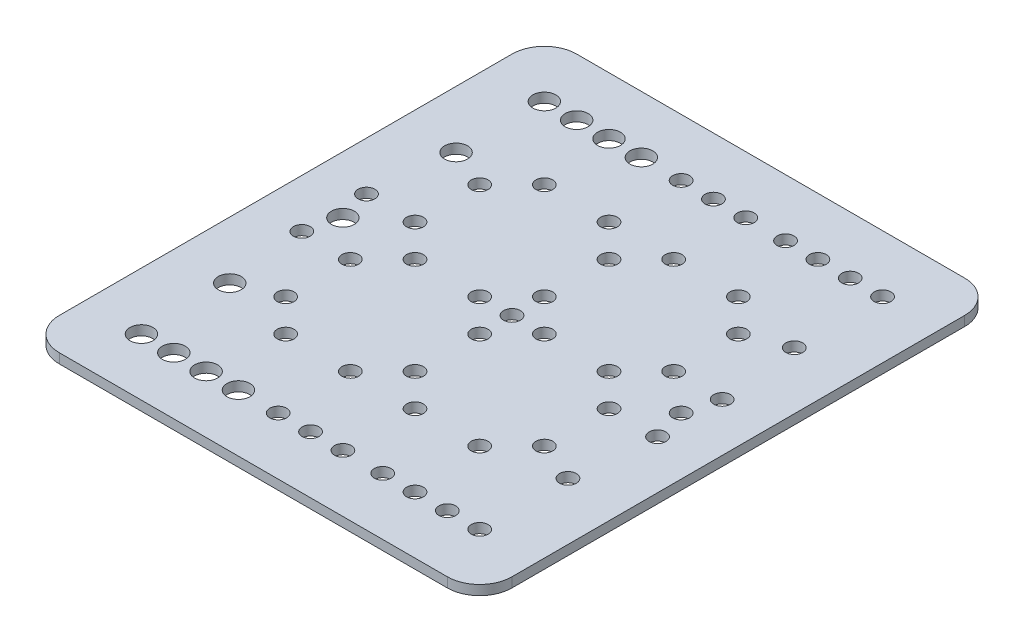
SolidWorks part; units mm, degrees
material "6061-T6 (SS)"
ref_plane "Front Plane" through (0, 0, 0) normal (0, 0, 1) x (1, 0, 0)
ref_plane "Top Plane" through (0, 0, 0) normal (0, 1, 0) x (1, 0, 0)
ref_plane "Right Plane" through (0, 0, 0) normal (1, 0, 0) x (0, 0, -1)
sketch "Sketch1" plane through (0, 0, 0) normal (0, 1, 0) x (1, 0, 0)
  line L0 (0, 0) -> (70, 0) construction
  line L1 (60, -80) -> (-60, -80)
  line L2 (70, -70) -> (70, 70)
  line L3 (60, 80) -> (-60, 80)
  line L4 (-70, -70) -> (-70, 70)
  line L5 (0, 80) -> (0, 0) construction
  arc A0 (-60, -80) -> (-70, -70) centre (-60, -70) cw
  arc A1 (60, -80) -> (70, -70) centre (60, -70) ccw
  arc A2 (70, 70) -> (60, 80) centre (60, 70) ccw
  arc A3 (-60, 80) -> (-70, 70) centre (-60, 70) ccw
  circle A4 centre (-42.3, 62.3) radius 3.55
  circle A5 centre (0, 10) radius 2.6
  circle A6 centre (0, 0) radius 2.6
  circle A7 centre (10, 0) radius 2.6
  circle A8 centre (-10, 0) radius 2.6
  circle A9 centre (-52.3, 62.3) radius 3.55
  circle A10 centre (-52.3, 0) radius 3.55
  circle A11 centre (-52.3, -62.3) radius 3.55
  circle A12 centre (-40, 30) radius 2.6
  circle A13 centre (-40, 10) radius 2.6
  circle A14 centre (-30, 40) radius 2.6
  circle A15 centre (0, 30) radius 2.6
  circle A16 centre (-10, 62.3) radius 2.6
  circle A17 centre (0, 62.3) radius 2.6
  circle A18 centre (10, 62.3) radius 2.6
  circle A19 centre (-10, 40) radius 2.6
  circle A20 centre (30, 40) radius 2.6
  circle A21 centre (40, 30) radius 2.6
  circle A22 centre (40, 10) radius 2.6
  circle A23 centre (42.3, 62.3) radius 2.6
  circle A24 centre (52.3, 62.3) radius 2.6
  circle A25 centre (52.3, 0) radius 2.6
  circle A26 centre (40, -10) radius 2.6
  circle A27 centre (52.3, -62.3) radius 2.6
  circle A28 centre (42.3, -62.3) radius 2.6
  circle A29 centre (40, -30) radius 2.6
  circle A30 centre (0, -10) radius 2.6
  circle A31 centre (30, -40) radius 2.6
  circle A32 centre (10, 40) radius 2.6
  circle A33 centre (10, -62.3) radius 2.6
  circle A34 centre (0, -62.3) radius 2.6
  circle A35 centre (-10, -62.3) radius 2.6
  circle A36 centre (30, 0) radius 2.6
  circle A37 centre (-30, -40) radius 2.6
  circle A38 centre (-40, -30) radius 2.6
  circle A39 centre (-40, -10) radius 2.6
  circle A40 centre (-42.3, -62.3) radius 3.55
  circle A41 centre (-32.3, 62.3) radius 3.55
  circle A42 centre (32.3, 62.3) radius 2.6
  circle A43 centre (22.3, -62.3) radius 2.6
  circle A44 centre (-30, 0) radius 2.6
  circle A45 centre (-52.3, 35) radius 3.55
  circle A46 centre (32.3, -62.3) radius 2.6
  circle A47 centre (-32.3, -62.3) radius 3.55
  circle A48 centre (-52.3, -35) radius 3.55
  circle A49 centre (52.3, 35) radius 2.6
  circle A50 centre (52.3, -35) radius 2.6
  circle A51 centre (-22.3, 62.3) radius 3.55
  circle A52 centre (22.3, 62.3) radius 2.6
  circle A53 centre (-22.3, -62.3) radius 3.55
  circle A54 centre (10, -40) radius 2.6
  circle A55 centre (-10, -40) radius 2.6
  circle A56 centre (0, -30) radius 2.6
  circle A57 centre (-55, 10) radius 2.6
  circle A58 centre (55, 10) radius 2.6
  circle A59 centre (55, -10) radius 2.6
  circle A60 centre (-55, -10) radius 2.6
  point P0 (0, 0)
  dimension "D2" = 10
  dimension "D3" = 5.2
  dimension "D5" = 7.1
  dimension "D7" = 10
  dimension "D10" = 10
  dimension "D19" = 10
  dimension "D1" = 160
  dimension "D4" = 10
  dimension "D6" = 124.6
  dimension "D8" = 17.7
  dimension "D9" = 140
  dimension "D11" = 30
  dimension "D12" = 30
  dimension "D13" = 27.3
  dimension "D14" = 40
  dimension "D15" = 10
  dimension "D16" = 104.6
  dimension "D17" = 10
  dimension "D18" = 10
  dimension "D20" = 15
  dimension "D21" = 40
  dimension "D22" = 10
  dimension "D23" = 10
extrude "Boss-Extrude1" add sketch "Sketch1" along normal blind 3
